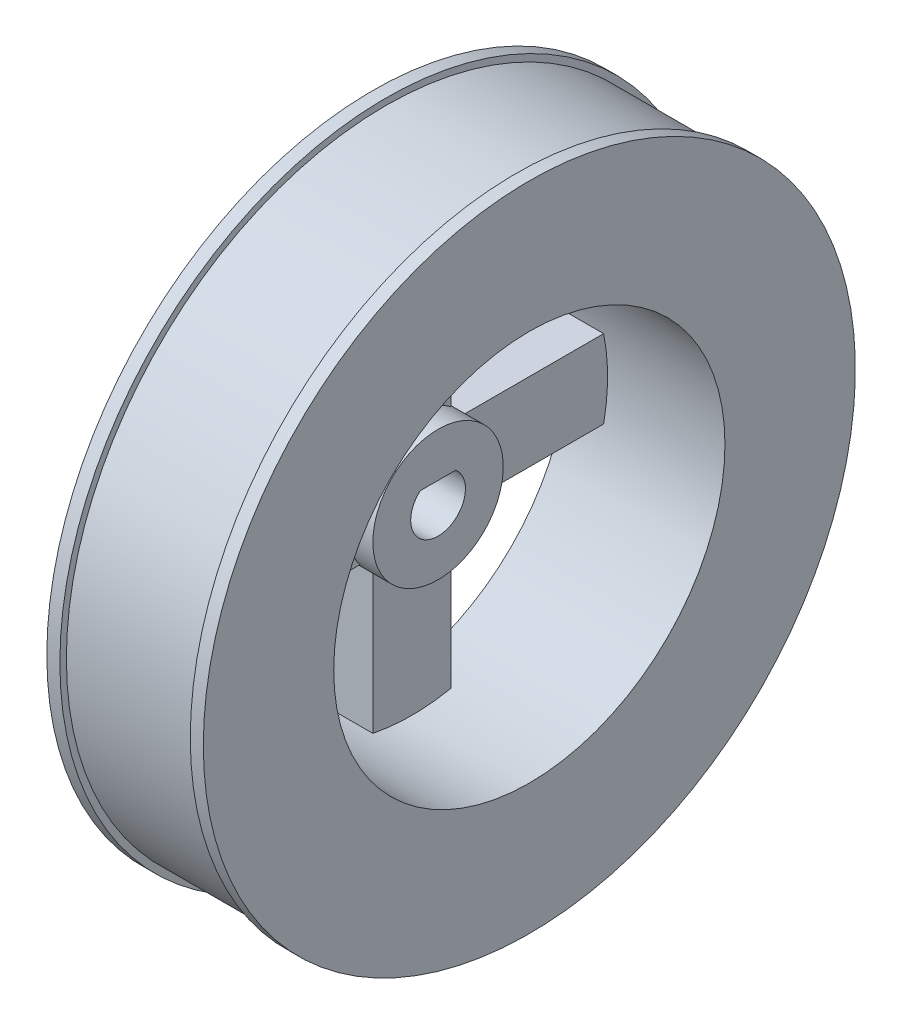
SolidWorks part; units mm, degrees
other "Markup1"
sketch "Sketch4" plane through (6, -25, -25) normal (1, 0, 0) x (0, 0, -1)
material "PLA (Black)"
ref_plane "Front Plane" through (0, 0, 0) normal (0, 0, 1) x (1, 0, 0)
ref_plane "Top Plane" through (0, 0, 0) normal (0, 1, 0) x (1, 0, 0)
ref_plane "Right Plane" through (0, 0, 0) normal (1, 0, 0) x (0, 0, -1)
sketch "Sketch1" plane through (0, 0, 0) normal (0, 0, 1) x (1, 0, 0)
  line L0 (0, 0) -> (41532.2986, 0) construction
  line L1 (-6, 25) -> (-6, 15)
  line L3 (6, 15) -> (6, 25)
  line L4 (6, 25) -> (5, 25)
  line L5 (5, 25) -> (5, 24.5)
  line L6 (5, 24.5) -> (-5, 24.5)
  line L7 (-5, 24.5) -> (-5, 25)
  line L8 (-5, 25) -> (-6, 25)
  line L9 (-6, 15) -> (6, 15)
  line L10 (-1, 5) -> (-6, 5)
  line L11 (-6, 5) -> (-6, 0)
  line L12 (-6, 0) -> (-1, 0)
  line L13 (-1, 0) -> (-1, 5)
  point P15 (0, 15)
  dimension "D1" = 50
  dimension "D2" = 0.5
  dimension "D3" = 1
  dimension "D4" = 10
  dimension "D5" = 10
  dimension "D6" = 10
  dimension "D7" = 5
revolve "Revolve1" add sketch "Sketch1" angle 360 about L0
sketch "Sketch2" plane through (-6, 0, 0) normal (1, 0, 0) x (0, 0, -1)
  line L2 (0, 0) -> (0, 50000) construction
  line L9 (-3, 4) -> (-3, 14.6969)
  line L10 (3, 4) -> (3, 14.6969)
  arc A0 (-3, 14.6969) -> (3, 14.6969) centre (0, 0) cw
  circle A12 centre (0, 0) radius 15 construction
  circle A13 centre (0, 0) radius 5
  arc A14 (3, 4) -> (-3, 4) centre (0, 0) ccw
  dimension "D2" = 6
  dimension "D3" = 0
extrude "Boss-Extrude1" add sketch "Sketch2" along normal blind 3
sketch "Sketch3" plane through (-1, 0, 0) normal (1, 0, 0) x (0, 0, -1)
  line L0 (-1.3601, 1.6) -> (1.3601, 1.6)
  arc A0 (-1.3601, 1.6) -> (1.3601, 1.6) centre (0, 0) ccw
  dimension "D1" = 4.2
  dimension "D2" = 1.6
extrude "Cut-Extrude1" cut sketch "Sketch3" against normal through all both and the other way through all
pattern_circular "CirPattern1" count 4 over 360 about axis through (0, 0, 0) along (1, 0, 0) of "Boss-Extrude1"
